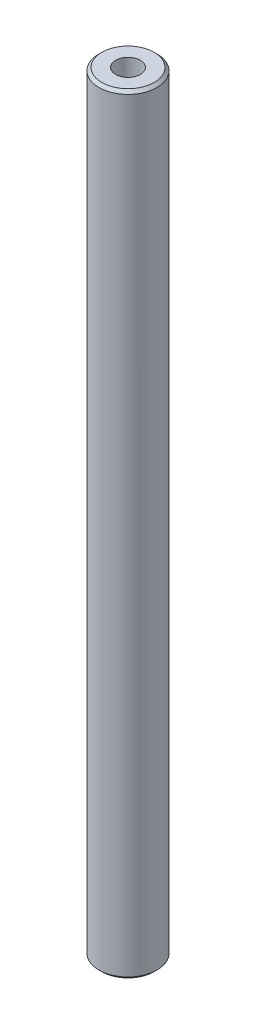
SolidWorks part; units mm, degrees
ref_plane "Front Plane" through (0, 0, 0) normal (0, 0, 1) x (1, 0, 0)
ref_plane "Top Plane" through (0, 0, 0) normal (0, 1, 0) x (1, 0, 0)
ref_plane "Right Plane" through (0, 0, 0) normal (1, 0, 0) x (0, 0, -1)
sketch "Sketch1" plane through (0, 0, 0) normal (0, 0, 1) x (1, 0, 0)
  line L0 (0, 132.5) -> (-10, 132.5)
  line L3 (-10, 132.5) -> (-10, -132.5)
  line L6 (-10, -132.5) -> (0, -132.5)
  line L7 (0, 132.5) -> (0, -132.5)
  dimension "D1" = 10
  dimension "D2" = 265
revolve "Revolve2" add sketch "Sketch1" angle 360 about L7
hole_wizard "M10 Tapped Hole1" positions "Sketch2" profile "Sketch3" tap size "M10" standard "ISO"
sketch "Sketch2" plane through (0, -132.5, 0) normal (0, -1, 0) x (-1, 0, 0)
  point P0 (0, 0)
sketch "Sketch3" plane through (0, -132.5, 0) normal (1, 0, 0) x (0, 0, -1)
  line L0 (0, 0) -> (0, 27.0537)
  line L1 (0, 27.0537) -> (4.25, 24.5)
  line L2 (4.25, 24.5) -> (4.25, 0)
  line L5 (4.25, 0) -> (0, 0)
  line L10 (0, 27.0537) -> (-4.25, 24.5) construction
  line L11 (0, -6.35) -> (0, 107.95) construction
  dimension "Tap Drill Dia." = 8.5
  dimension "Tap Drill Depth" = 24.5
  dimension "Drill Angle" = 118
cosmetic thread "Hole Thread1" parameters "D1"=20, "D2"=10
mirror "Mirror1" about plane through (0, 0, 0) normal (0, 1, 0) of "M10 Tapped Hole1"
cosmetic thread "Hole Thread2" parameters "D1"=20, "D2"=10
chamfer "Chamfer1" distance 1 angle 45 2 edges at (0, 132.5, 10) (0, -132.5, 10)
